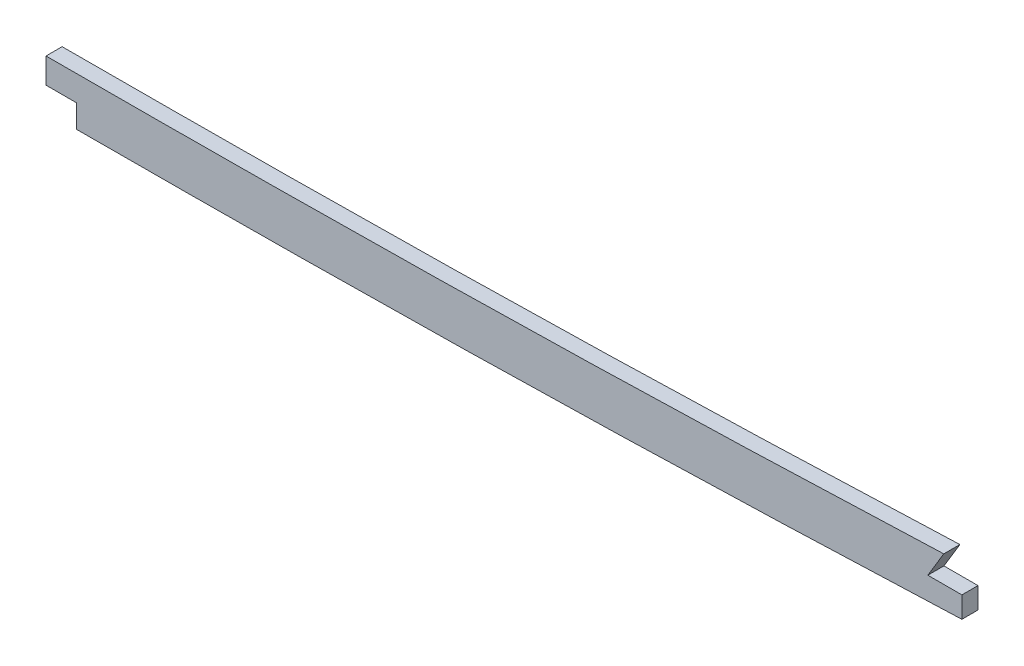
SolidWorks part; units mm, degrees
ref_plane "Front Plane" through (0, 0, 0) normal (0, 0, 1) x (1, 0, 0)
ref_plane "Top Plane" through (0, 0, 0) normal (0, 1, 0) x (1, 0, 0)
ref_plane "Right Plane" through (0, 0, 0) normal (1, 0, 0) x (0, 0, -1)
sketch "Sketch1" plane through (0, 0, 0) normal (0, 0, 1) x (1, 0, 0)
  line L0 (1046.2855, 53.4707) -> (499.61, 53.4707) construction
  line L1 (55, 0) -> (-55, 0) construction
  line L2 (1046.2855, -53.4707) -> (499.61, -53.4707)
  line L3 (1046.2855, -34.4207) -> (499.61, -34.4207)
  line L4 (99.06, -18.1493) -> (99.06, -37.7415)
  line L5 (2669.54, 9.5231) -> (2669.54, -9.569)
  spline S0 degree 5 poles (2699.7923, 7.5245) (2639.6368, 11.6572) (2579.4813, 15.4358) (2518.4981, 19.1485) (2436.3555, 23.2524) (2354.213, 26.6315) (2332.5703, 27.481) (2156.2686, 34.3778) (1979.9669, 41.6286) (1824.1143, 52.7713) (1636.9286, 53.5796) (1449.7429, 53.454) (1418.0067, 53.4707) (1324.8993, 53.4707) (1231.7919, 53.4707) (1170.4413, 53.4707) (1108.7841, 53.4707) (1047.1269, 53.4707) (1046.8464, 53.4707) (1046.5659, 53.4707) (1046.2855, 53.4707) knots 100.654805 100.654805 100.654805 100.654805 100.654805 100.654805 130.927897 130.927897 130.927897 141.337055 141.337055 141.337055 218.101815 218.101815 218.101815 233.772059 233.772059 233.772059 264.077723 264.077723 264.077723 264.216209 264.216209 264.216209 264.216209 264.216209 264.216209 weights 1 1 1 1 1 1 1 1 1 1 1 1 1 1 1 1 1 1 1 1 1 construction
  spline S1 degree 5 poles (499.61, 53.4707) (492.1368, 53.4707) (484.7543, 53.4707) (477.443, 53.4707) (448.5166, 53.4707) (419.5901, 53.4707) (398.3681, 53.4707) (355.6475, 53.4707) (312.927, 53.4707) (289.2351, 53.4703) (265.365, 53.4707) (241.4948, 53.4707) (241.4716, 53.4707) (241.4484, 53.4707) (241.4251, 53.4707) knots 19.90683 19.90683 19.90683 19.90683 19.90683 19.90683 23.637897 23.637897 23.637897 34.276546 34.276546 34.276546 46.401341 46.401341 46.401341 46.413154 46.413154 46.413154 46.413154 46.413154 46.413154 weights 1 1 1 1 1 1 1 1 1 1 1 1 1 1 1 construction
  spline S2 degree 5 poles (241.4251, 53.4707) (224.2869, 53.4707) (207.1495, 53.4673) (190.2039, 52.6866) (151.6561, 49.0319) (113.1083, 41.5037) (91.9499, 36.3426) (71.313, 30.9696) (50.6762, 24.7565) knots 0 0 0 0 0 0 8.713816 8.713816 8.713816 19.90683 19.90683 19.90683 19.90683 19.90683 19.90683 weights 1 1 1 1 1 1 1 1 1 construction
  spline S3 degree 5 poles (241.4251, -53.4707) (224.2869, -53.4707) (207.1495, -53.4673) (190.2039, -52.6866) (151.6561, -49.0319) (113.1083, -41.5037) (91.9499, -36.3426) (71.313, -30.9696) (50.6762, -24.7565) knots 0 0 0 0 0 0 8.713816 8.713816 8.713816 19.90683 19.90683 19.90683 19.90683 19.90683 19.90683 weights 1 1 1 1 1 1 1 1 1
  spline S4 degree 5 poles (499.61, -53.4707) (492.1368, -53.4707) (484.7543, -53.4707) (477.443, -53.4707) (448.5166, -53.4707) (419.5901, -53.4707) (398.3681, -53.4707) (355.6475, -53.4707) (312.927, -53.4707) (289.2351, -53.4703) (265.365, -53.4707) (241.4948, -53.4707) (241.4716, -53.4707) (241.4484, -53.4707) (241.4251, -53.4707) knots 19.90683 19.90683 19.90683 19.90683 19.90683 19.90683 23.637897 23.637897 23.637897 34.276546 34.276546 34.276546 46.401341 46.401341 46.401341 46.413154 46.413154 46.413154 46.413154 46.413154 46.413154 weights 1 1 1 1 1 1 1 1 1 1 1 1 1 1 1
  spline S5 degree 5 poles (2699.7923, -7.5245) (2639.6368, -11.6572) (2579.4813, -15.4358) (2518.4981, -19.1485) (2436.3555, -23.2524) (2354.213, -26.6315) (2332.5703, -27.481) (2156.2686, -34.3778) (1979.9669, -41.6286) (1824.1143, -52.7713) (1636.9286, -53.5796) (1449.7429, -53.454) (1418.0067, -53.4707) (1324.8993, -53.4707) (1231.7919, -53.4707) (1170.4413, -53.4707) (1108.7841, -53.4707) (1047.1269, -53.4707) (1046.8464, -53.4707) (1046.5659, -53.4707) (1046.2855, -53.4707) knots 100.654805 100.654805 100.654805 100.654805 100.654805 100.654805 130.927897 130.927897 130.927897 141.337055 141.337055 141.337055 218.101815 218.101815 218.101815 233.772059 233.772059 233.772059 264.077723 264.077723 264.077723 264.216209 264.216209 264.216209 264.216209 264.216209 264.216209 weights 1 1 1 1 1 1 1 1 1 1 1 1 1 1 1 1 1 1 1 1 1
  spline S6 degree 1 poles (2698.4867, 11.4807) (1046.2855, -34.4207) knots 0 0 1 1 construction
  spline S7 degree 1 poles (499.61, -34.4207) (241.4252, -34.4207) knots 0 0 1 1 construction
  spline S8 degree 1 poles (241.4252, -34.4207) (56.168, -6.5153) knots 0 0 1 1 construction
  spline S9 degree 3 poles (2698.4867, 11.4807) (2691.2474, 10.9833) (2679.1952, 10.1655) (2662.2765, 9.0388) (2635.6663, 7.2925) (2596.8577, 4.8261) (2545.7297, 1.7583) (2494.4053, -1.0986) (2451.533, -3.2666) (2417.1983, -4.8671) (2391.4571, -6.0036) (2365.6347, -7.0869) (2339.5463, -8.1377) (2313.4661, -9.1651) (2287.6124, -10.1795) (2261.7633, -11.201) (2227.2853, -12.5838) (2184.1756, -14.3661) (2132.4291, -16.6074) (2063.4255, -19.7089) (1977.1749, -23.7005) (1873.7325, -28.1494) (1770.3746, -31.6575) (1667.0857, -33.7931) (1581.0111, -34.3832) (1512.074, -34.4278) (1443.0615, -34.4095) (1356.8009, -34.4244) (1218.7946, -34.4185) (1115.289, -34.4207) (1046.2855, -34.4207) knots 100.654805 100.654805 100.654805 100.654805 102.842388 104.300777 105.766098 110.877392 115.988686 121.09998 126.211274 128.766921 131.322568 133.878215 136.433862 138.989509 141.545156 144.100803 146.656449 151.767743 156.879037 161.990331 172.212919 182.435507 192.658094 202.880682 213.10327 218.214564 223.325858 233.548445 243.771033 264.216209 264.216209 264.216209 264.216209
  spline S10 degree 3 poles (499.61, -34.4207) (488.6147, -34.4207) (472.2364, -34.4207) (449.9402, -34.4207) (427.7713, -34.4207) (405.8747, -34.4207) (384.5849, -34.4207) (368.9002, -34.4207) (353.3766, -34.4207) (332.6085, -34.4207) (306.2878, -34.4206) (274.0235, -34.4205) (252.271, -34.4207) (241.4252, -34.4207) knots 19.90683 19.90683 19.90683 19.90683 23.22012 24.876765 26.533411 29.846701 31.503346 33.159992 34.816637 36.473282 39.786573 43.099863 46.413154 46.413154 46.413154 46.413154
  spline S11 degree 3 poles (241.4252, -34.4207) (239.3949, -34.4207) (235.3223, -34.4205) (227.2744, -34.3987) (217.3194, -34.2975) (205.5307, -33.9764) (189.9633, -33.2126) (170.697, -31.5435) (147.5333, -28.3144) (125.4828, -24.2021) (107.4399, -20.1965) (92.2061, -16.4882) (75.9505, -12.2555) (63.6202, -8.7589) (56.168, -6.5153) knots 0 0 0 0 0.622088 1.244177 2.488354 3.732531 4.976707 7.465061 9.953415 12.441768 14.558235 15.802412 17.418476 19.90683 19.90683 19.90683 19.90683
  point P2 (0, 0)
  dimension "D1" = 50.6762
  dimension "D3" = 99.06
  dimension "D4" = 2669.54
  dimension "D2" = 19.05
extrude "Boss-Extrude1" add sketch "Sketch1" along normal mid plane 6.35 contours S10 S11 L4 S3 S4 L2 S5 L5 S9 L3
sketch "Sketch2" plane through (0, 0, 3.175) normal (0, 0, 1) x (1, 0, 0)
  line L0 (2187.01, -14.2633) -> (2312.9875, -14.2633)
  line L1 (2312.9875, -14.2633) -> (2312.9875, -9.1833)
  spline S0 degree 3 poles (689.0175, 232.3189) (4033.8285, 148.9311) (3356.6623, 54.6077) (2635.6663, 7.2925) (2596.8577, 4.8261) (2545.7297, 1.7583) (2494.4053, -1.0986) (2451.533, -3.2666) (2417.1983, -4.8671) (2391.4571, -6.0036) (2365.6347, -7.0869) (2339.5463, -8.1377) (2313.4661, -9.1651) (2287.6124, -10.1795) (2261.7633, -11.201) (2227.2853, -12.5838) (2184.1756, -14.3661) (2132.4291, -16.6074) (2063.4255, -19.7089) (1977.1749, -23.7005) (1873.7325, -28.1494) (1770.3746, -31.6575) (1667.0857, -33.7931) (1581.0111, -34.3832) (1512.074, -34.4278) (1443.0615, -34.4095) (1356.8009, -34.4244) (551.9641, -34.3896) (-218.4198, -34.7282) (-953.6342, -29.9632) knots -106.828462 -106.828462 -106.828462 -106.828462 104.300777 105.766098 110.877392 115.988686 121.09998 126.211274 128.766921 131.322568 133.878215 136.433862 138.989509 141.545156 144.100803 146.656449 151.767743 156.879037 161.990331 172.212919 182.435507 192.658094 202.880682 213.10327 218.214564 223.325858 233.548445 243.771033 461.793666 461.793666 461.793666 461.793666 only from (2669.54, 9.5231) to (1046.2855, -34.4207) construction
  spline S1 degree 3 poles (2669.54, 9.5231) (2667.1265, 9.3624) (2659.8616, 8.8803) (2635.6663, 7.2925) (2596.8577, 4.8261) (2545.7297, 1.7583) (2494.4053, -1.0986) (2451.533, -3.2666) (2417.1983, -4.8671) (2391.4571, -6.0036) (2365.6347, -7.0869) (2339.5463, -8.1377) (2313.4661, -9.1651) (2287.6124, -10.1795) (2261.7633, -11.201) (2227.2853, -12.5838) (2184.1756, -14.3661) (2132.4291, -16.6074) (2063.4255, -19.7089) (1977.1749, -23.7005) (1873.7325, -28.1494) (1770.3746, -31.6575) (1667.0857, -33.7931) (1581.0111, -34.3832) (1512.074, -34.4278) (1443.0615, -34.4095) (1356.8009, -34.4244) (1218.7946, -34.4185) (1115.289, -34.4207) (1046.2855, -34.4207) knots 103.571583 103.571583 103.571583 103.571583 104.300777 105.766098 110.877392 115.988686 121.09998 126.211274 128.766921 131.322568 133.878215 136.433862 138.989509 141.545156 144.100803 146.656449 151.767743 156.879037 161.990331 172.212919 182.435507 192.658094 202.880682 213.10327 218.214564 223.325858 233.548445 243.771033 264.216209 264.216209 264.216209 264.216209
  point P2 (0, 0)
  spline M9 degree 3 poles (2698.4867, 11.4807) (2691.2474, 10.9833) (2679.1952, 10.1655) (2662.2765, 9.0388) (2635.6663, 7.2925) (2596.8577, 4.8261) (2545.7297, 1.7583) (2494.4053, -1.0986) (2451.533, -3.2666) (2417.1983, -4.8671) (2391.4571, -6.0036) (2365.6347, -7.0869) (2339.5463, -8.1377) (2313.4661, -9.1651) (2287.6124, -10.1795) (2261.7633, -11.201) (2227.2853, -12.5838) (2184.1756, -14.3661) (2132.4291, -16.6074) (2063.4255, -19.7089) (1977.1749, -23.7005) (1873.7325, -28.1494) (1770.3746, -31.6575) (1667.0857, -33.7931) (1581.0111, -34.3832) (1512.074, -34.4278) (1443.0615, -34.4095) (1356.8009, -34.4244) (1218.7946, -34.4185) (1115.289, -34.4207) (1046.2855, -34.4207) knots 100.654805 100.654805 100.654805 100.654805 102.842388 104.300777 105.766098 110.877392 115.988686 121.09998 126.211274 128.766921 131.322568 133.878215 136.433862 138.989509 141.545156 144.100803 146.656449 151.767743 156.879037 161.990331 172.212919 182.435507 192.658094 202.880682 213.10327 218.214564 223.325858 233.548445 243.771033 264.216209 264.216209 264.216209 264.216209 only from (2669.54, 9.5231) to (1046.2855, -34.4207)
  dimension "D1" = 2312.9875
  dimension "D2" = 5.08
extrude "Cut-Extrude1" cut sketch "Sketch2" against normal through all contours L0 L1 M9
fillet "Fillet1" radius 2.54 6 edges at (2669.54, -9.569, 0) (2669.54, 9.5231, 0) (99.06, -37.7415, 0) (99.06, -18.1493, 0) (2312.9875, -14.2633, 0)
sketch "Sketch3" plane through (0, 0, 3.175) normal (0, 0, 1) x (1, 0, 0)
  line L19 (1534.5209, -34.4089) -> (1534.5209, -44.3802)
  line L20 (1534.5209, -44.3802) -> (1546.518, -44.3802)
  line L21 (1546.518, -44.3802) -> (1546.518, -53.4448)
  line L22 (1888.275, -27.4246) -> (1881.9861, -37.8581)
  line L23 (1881.9861, -37.8581) -> (1895.4063, -37.8581)
  line L24 (1895.4063, -37.8581) -> (1895.4063, -46.2049)
  line L28 (1534.5209, -34.4089) -> (1534.5209, 89.7671)
  line L29 (1534.5209, 89.7671) -> (0, 180.9997)
  line L30 (0, 180.9997) -> (55.6934, -302.6239)
  line L31 (55.6934, -302.6239) -> (1546.518, -106.0232)
  line L32 (1546.518, -106.0232) -> (1546.518, -53.4448)
  line L33 (1888.275, -27.4246) -> (1888.275, 63.1303)
  line L34 (1888.275, 63.1303) -> (2711.7034, 52.2917)
  line L35 (2711.7034, 52.2917) -> (2711.7034, -53.4448)
  line L36 (2711.7034, -53.4448) -> (1895.4063, -56.6644)
  line L37 (1895.4063, -56.6644) -> (1895.4063, -46.2049)
  spline S2 degree 3 poles (2187.01, -14.2633) (2186.0643, -14.3032) (2167.8725, -15.0722) (2132.4291, -16.6074) (2063.4255, -19.7089) (1977.1749, -23.7005) (1873.7325, -28.1494) (1770.3746, -31.6575) (1667.0857, -33.7931) (1581.0111, -34.3832) (1512.074, -34.4278) (1443.0615, -34.4095) (1356.8009, -34.4244) (1218.7946, -34.4185) (1115.289, -34.4207) (1046.2855, -34.4207) knots 151.487489 151.487489 151.487489 151.487489 151.767743 156.879037 161.990331 172.212919 182.435507 192.658094 202.880682 213.10327 218.214564 223.325858 233.548445 243.771033 264.216209 264.216209 264.216209 264.216209 construction
  spline S3 degree 5 poles (2667.1682, -9.7266) (2613.4902, -13.2886) (2559.6385, -16.6207) (2505.242, -19.8061) (2429.7275, -23.525) (2354.213, -26.6315) (2332.5703, -27.481) (2156.2686, -34.3778) (1979.9669, -41.6286) (1824.1143, -52.7713) (1636.9286, -53.5796) (1449.7429, -53.454) (1418.0067, -53.4707) (1324.8993, -53.4707) (1231.7919, -53.4707) (1170.4413, -53.4707) (1108.7841, -53.4707) (1047.1269, -53.4707) (1046.8464, -53.4707) (1046.5659, -53.4707) (1046.2855, -53.4707) knots 103.937447 103.937447 103.937447 103.937447 103.937447 103.937447 130.927897 130.927897 130.927897 141.337055 141.337055 141.337055 218.101815 218.101815 218.101815 233.772059 233.772059 233.772059 264.077723 264.077723 264.077723 264.216209 264.216209 264.216209 264.216209 264.216209 264.216209 weights 1 1 1 1 1 1 1 1 1 1 1 1 1 1 1 1 1 1 1 1 1 construction
extrude "Cut-Extrude2" cut sketch "Sketch3" against normal blind 7.62
